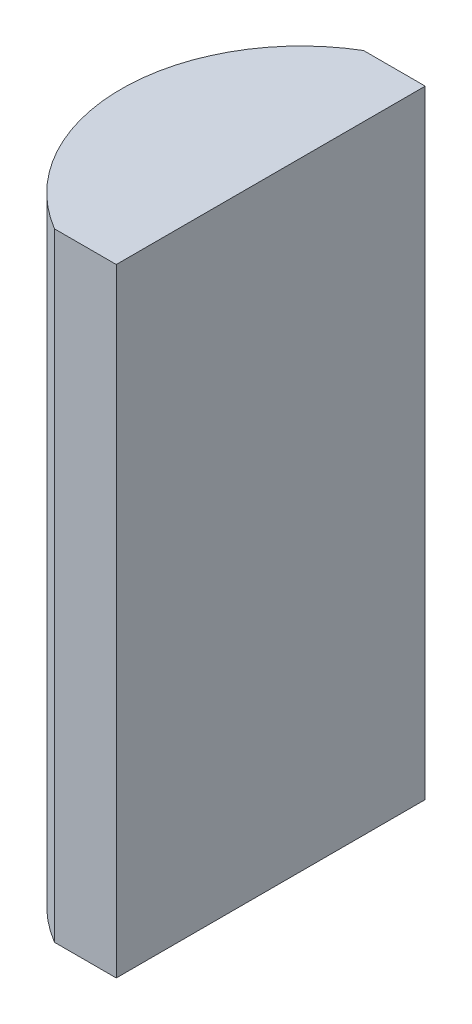
SolidWorks part; units mm, degrees
ref_plane "前视基准面" through (0, 0, 0) normal (0, 0, 1) x (1, 0, 0)
ref_plane "上视基准面" through (0, 0, 0) normal (0, 1, 0) x (1, 0, 0)
ref_plane "右视基准面" through (0, 0, 0) normal (1, 0, 0) x (0, 0, -1)
sketch "草图1" plane through (0, 0, 0) normal (0, 1, 0) x (1, 0, 0)
  line L0 (-137.6835, 0) -> (10.8051, 0) construction
  line L1 (1.3765, 5) -> (3.3752, 5)
  line L2 (1.3765, -5) -> (3.3752, -5)
  line L3 (3.3752, 5) -> (3.3752, -5)
  arc A0 (1.3765, 5) -> (1.3765, -5) centre (4.3552, 0) ccw
  point P2 (-1.4648, 0)
  point P4 (3.3752, 0)
  dimension "D2" = 5
  dimension "D3" = 5.82
  dimension "D4" = 4.84
  dimension "D1" = 5
extrude "凸台-拉伸1" add sketch "草图1" along normal blind 20
